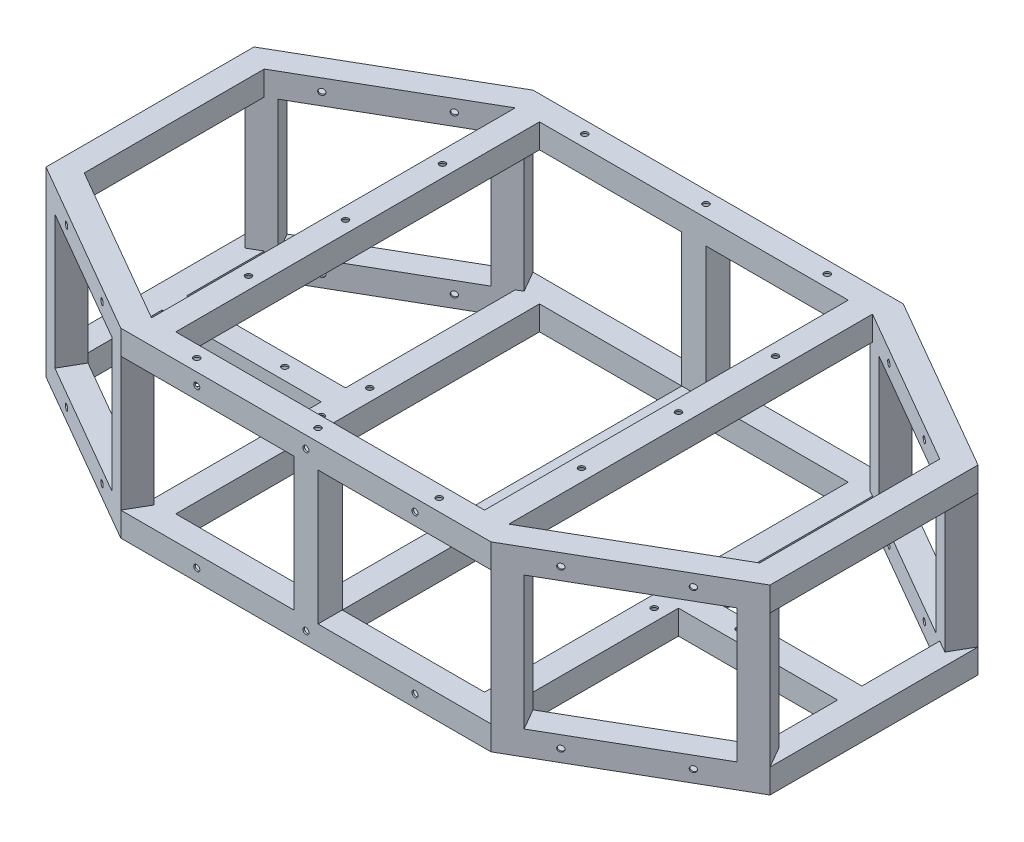
SolidWorks part; units mm, degrees
material "6061-T6 (SS)"
ref_plane "Front Plane" through (0, 0, 0) normal (0, 0, 1) x (1, 0, 0)
ref_plane "Top Plane" through (0, 0, 0) normal (0, 1, 0) x (1, 0, 0)
ref_plane "Right Plane" through (0, 0, 0) normal (1, 0, 0) x (0, 0, -1)
sketch "Sketch1" plane through (0, 0, 0) normal (1, 0, 0) x (0, 0, -1)
  line L1 (190.5, -12.7) -> (215.9, -12.7)
  line L2 (190.5, -12.7) -> (190.5, 12.7)
  line L3 (190.5, 12.7) -> (215.9, 12.7)
  line L4 (215.9, -12.7) -> (215.9, 12.7)
  line L5 (190.5, -12.7) -> (215.9, 12.7) construction
  line L6 (190.5, 12.7) -> (215.9, -12.7) construction
  line L7 (192.151, -11.049) -> (214.249, -11.049)
  line L8 (192.151, -11.049) -> (192.151, 11.049)
  line L9 (192.151, 11.049) -> (214.249, 11.049)
  line L10 (214.249, -11.049) -> (214.249, 11.049)
  line L11 (192.151, -11.049) -> (214.249, 11.049) construction
  line L12 (192.151, 11.049) -> (214.249, -11.049) construction
  point P0 (203.2, 0)
  point P5 (203.2, 0)
  dimension "D1" = 203.2
  dimension "D2" = 25.4
  dimension "D3" = 25.4
  dimension "D4" = 1.651
sketch "Sketch2" plane through (0, 0, 0) normal (0, 1, 0) x (1, 0, 0)
  line L0 (0, 0) -> (-366.4764, 0) construction
  line L1 (0, 0) -> (0, 203.2) construction
  line L2 (190.5, 203.2) -> (-190.5, 203.2)
  line L3 (-190.5, 203.2) -> (-366.4764, 101.6)
  line L4 (-366.4764, 101.6) -> (-366.4764, -101.6)
  line L5 (-366.4764, -101.6) -> (-190.5, -203.2)
  line L6 (-190.5, -203.2) -> (190.5, -203.2)
  line L7 (190.5, 203.2) -> (366.4764, 101.6)
  line L8 (366.4764, 101.6) -> (366.4764, -101.6)
  line L9 (366.4764, -101.6) -> (190.5, -203.2)
  dimension "D1" = 203.2
  dimension "D2" = 381
  dimension "D3" = 30
  dimension "D4" = 203.2
  dimension "D5" = 203.2
sweep "Sweep2" add profiles "Sketch1" path "Sketch2"
sketch "Sketch4" plane through (0, 12.7, 0) normal (0, 1, 0) x (1, 0, 0)
  line L0 (-193.903, -215.9) -> (-215.9, -203.2)
  line L1 (-193.903, -215.9) -> (-181.203, -193.903)
  line L2 (-215.9, -203.2) -> (-203.2, -181.203)
  line L3 (-181.203, -193.903) -> (-203.2, -181.203)
  line L4 (-379.1764, -108.9323) -> (-193.903, -215.9) construction
  line L5 (-213.6447, -202.5957) -> (-202.5957, -183.4583)
  line L6 (-183.4583, -194.5073) -> (-202.5957, -183.4583)
  line L7 (-194.5073, -213.6447) -> (-183.4583, -194.5073)
  line L8 (-194.5073, -213.6447) -> (-213.6447, -202.5957)
  dimension "D1" = 25.4
  dimension "D2" = 25.4
  dimension "D3" = 1.651
extrude "Vertical Member" add sketch "Sketch4" along normal blind 139.7
sketch "Sketch5" plane through (0, 12.7, 0) normal (0, 1, 0) x (1, 0, 0)
  line L0 (-379.1764, -108.9323) -> (-357.1793, -121.6323)
  line L1 (-379.1764, -108.9323) -> (-366.4764, -86.9353)
  line L2 (-357.1793, -121.6323) -> (-344.4793, -99.6353)
  line L3 (-366.4764, -86.9353) -> (-344.4793, -99.6353)
  line L4 (-379.1764, -108.9323) -> (-215.9, -203.2) construction
  line L6 (-376.9211, -108.328) -> (-357.7836, -119.377)
  line L7 (-357.7836, -119.377) -> (-346.7346, -100.2396)
  line L8 (-365.8721, -89.1906) -> (-346.7346, -100.2396)
  line L9 (-376.9211, -108.328) -> (-365.8721, -89.1906)
  dimension "D1" = 25.4
  dimension "D2" = 25.4
  dimension "D3" = 1.651
extrude "Vertical Member 2" add sketch "Sketch5" along normal blind 139.7
mirror "Mirror1" about plane through (0, 0, 0) normal (0, 0, 1) of "Vertical Member 2", "Vertical Member"
mirror "Mirror2" about plane through (0, 0, 0) normal (1, 0, 0) of "Mirror1", "Vertical Member", "Vertical Member 2"
sketch "Sketch6" plane through (0, 12.7, 0) normal (0, 1, 0) x (1, 0, 0)
  line L0 (0, -203.2) -> (0, 0) construction
  line L1 (-190.5, -203.2) -> (190.5, -203.2) construction
  line L2 (-187.097, -190.5) -> (187.097, -190.5) construction
  line L3 (-12.7, -215.9) -> (12.7, -215.9)
  line L4 (-12.7, -215.9) -> (-12.7, -190.5)
  line L5 (-12.7, -190.5) -> (12.7, -190.5)
  line L6 (12.7, -215.9) -> (12.7, -190.5)
  line L7 (-12.7, -215.9) -> (12.7, -190.5) construction
  line L8 (-12.7, -190.5) -> (12.7, -215.9) construction
  line L9 (-11.049, -192.151) -> (11.049, -192.151)
  line L10 (11.049, -214.249) -> (11.049, -192.151)
  line L11 (-11.049, -214.249) -> (11.049, -214.249)
  line L12 (-11.049, -214.249) -> (-11.049, -192.151)
  dimension "D1" = 25.4
  dimension "D2" = 1.651
extrude "Boss-Extrude3" add sketch "Sketch6" along normal blind 139.7
mirror "Mirror3" about plane through (0, 0, 0) normal (0, 0, 1) of "Boss-Extrude3"
ref_plane "Plane1" through (0, 82.55, 0) normal (0, 1, 0) x (1, 0, 0)
mirror "Mirror4" about plane through (0, 82.55, 0) normal (0, 1, 0) of "Sweep2"
sketch "Sketch7" plane through (0, 0, 190.5) normal (0, 0, -1) x (-1, 0, 0)
  line L0 (-11.049, -11.049) -> (-11.049, 11.049)
  line L1 (-12.7, -12.7) -> (12.7, -12.7)
  line L2 (-12.7, -12.7) -> (-12.7, 12.7)
  line L3 (-12.7, 12.7) -> (12.7, 12.7)
  line L4 (12.7, -12.7) -> (12.7, 12.7)
  line L5 (-12.7, -12.7) -> (12.7, 12.7) construction
  line L6 (-12.7, 12.7) -> (12.7, -12.7) construction
  line L7 (-11.049, 11.049) -> (11.049, 11.049)
  line L8 (11.049, -11.049) -> (11.049, 11.049)
  line L9 (-11.049, -11.049) -> (11.049, -11.049)
  point P0 (0, 0)
  dimension "D1" = 25.4
  dimension "D2" = 25.4
  dimension "D3" = 1.651
extrude "Boss-Extrude4" add sketch "Sketch7" along normal up to next
sketch "Sketch8" plane through (0, 0, 190.5) normal (0, 0, -1) x (-1, 0, 0)
  line L0 (-187.097, -12.7) -> (-187.097, 12.7)
  line L1 (-187.097, -12.7) -> (-161.697, -12.7)
  line L2 (-187.097, 12.7) -> (-161.697, 12.7)
  line L3 (-161.697, -12.7) -> (-161.697, 12.7)
  line L4 (-163.348, -11.049) -> (-163.348, 11.049)
  line L5 (-185.446, 11.049) -> (-163.348, 11.049)
  line L6 (-185.446, -11.049) -> (-185.446, 11.049)
  line L7 (-185.446, -11.049) -> (-163.348, -11.049)
  dimension "D1" = 25.4
  dimension "D2" = 25.4
  dimension "D3" = 1.651
extrude "Boss-Extrude5" add sketch "Sketch8" along normal up to next (381 mm away)
sketch "Sketch9" plane through (353.7764, 0, 0) normal (-1, 0, 0) x (0, 0, 1)
  line L0 (94.2677, 12.7) -> (-94.2677, 12.7) construction
  line L1 (-12.7, -12.7) -> (12.7, -12.7)
  line L2 (-12.7, -12.7) -> (-12.7, 12.7)
  line L3 (-12.7, 12.7) -> (12.7, 12.7)
  line L4 (12.7, -12.7) -> (12.7, 12.7)
  line L5 (-12.7, -12.7) -> (12.7, 12.7) construction
  line L6 (-12.7, 12.7) -> (12.7, -12.7) construction
  line L7 (-11.049, 11.049) -> (11.049, 11.049)
  line L8 (11.049, -11.049) -> (11.049, 11.049)
  line L9 (-11.049, -11.049) -> (11.049, -11.049)
  line L10 (-11.049, -11.049) -> (-11.049, 11.049)
  point P0 (0, 0)
  dimension "D1" = 25.4
  dimension "D2" = 1.651
extrude "Boss-Extrude6" add sketch "Sketch9" along normal up to next (166.6793 mm away)
mirror "Mirror5" about plane through (0, 0, 0) normal (1, 0, 0) of "Boss-Extrude5", "Boss-Extrude6"
sketch "Sketch10" plane through (0, 0, -190.5) normal (0, 0, 1) x (1, 0, 0)
  line L0 (-187.097, 177.8) -> (-187.097, 152.4)
  line L1 (-187.097, 177.8) -> (-161.697, 177.8)
  line L2 (-187.097, 152.4) -> (-161.697, 152.4)
  line L3 (-161.697, 177.8) -> (-161.697, 152.4)
  line L4 (-185.446, 154.051) -> (-163.348, 154.051)
  line L5 (-163.348, 176.149) -> (-163.348, 154.051)
  line L6 (-185.446, 176.149) -> (-163.348, 176.149)
  line L7 (-185.446, 176.149) -> (-185.446, 154.051)
  dimension "D1" = 25.4
  dimension "D2" = 25.4
  dimension "D3" = 1.651
extrude "Boss-Extrude7" add sketch "Sketch10" along normal up to next (381 mm away)
mirror "Mirror6" about plane through (0, 0, 0) normal (1, 0, 0) of "Boss-Extrude7"
sketch "Sketch12" plane through (-141.9632, 0, 245.8874) normal (-0.5, 0, 0.866) x (0.866, 0, 0.5)
  line L0 (-215.119, 165.1) -> (-113.519, 165.1) construction
  line L1 (-248.5102, 152.4) -> (-85.3749, 152.4) construction
  dimension "D1" = 12.7
  dimension "D2" = 101.6
sketch "Sketch14" plane through (-141.9632, 0, 245.8874) normal (-0.5, 0, 0.866) x (0.866, 0, 0.5)
  point P0 (-215.119, 165.1)
  point P1 (-113.519, 165.1)
hole_wizard "1/4 (0.25) Diameter Hole1" positions "Sketch18" profile "Sketch19" hole size "1/4" standard "ANSI Inch"
sketch "Sketch18" plane through (-141.9632, 0, 245.8874) normal (-0.5, 0, 0.866) x (0.866, 0, 0.5)
  point P0 (-215.119, 165.1)
  point P3 (-113.519, 165.1)
sketch "Sketch19" plane through (-328.2617, 165.1, 138.3279) normal (0, 1, 0) x (0.866, 0, 0.5)
  line L0 (0, 0) -> (0, 52.7077)
  line L1 (0, 52.7077) -> (3.175, 50.8)
  line L2 (3.175, 50.8) -> (3.175, 0)
  line L5 (3.175, 0) -> (0, 0)
  line L10 (0, 52.7077) -> (-3.175, 50.8) construction
  line L11 (0, -6.35) -> (0, 107.95) construction
  dimension "Hole Dia." = 6.35
  dimension "Hole Depth" = 50.8
  dimension "Drill Angle" = 118
mirror "Mirror7" about plane through (0, 82.55, 0) normal (0, 1, 0) of "1/4 (0.25) Diameter Hole1"
mirror "Mirror8" about plane through (0, 0, 0) normal (0, 0, 1) of "Mirror7", "1/4 (0.25) Diameter Hole1"
mirror "Mirror9" about plane through (0, 0, 0) normal (1, 0, 0) of "Mirror8", "Mirror7", "1/4 (0.25) Diameter Hole1"
sketch "Sketch20" plane through (0, 12.7, 0) normal (0, 1, 0) x (1, 0, 0)
  line L0 (-161.697, -190.5) -> (-12.7, -190.5) construction
  line L1 (-187.097, -190.5) -> (-187.097, 190.5) construction
  line L2 (-187.097, 190.5) -> (-187.097, 12.7) construction
  line L3 (-187.097, 12.7) -> (-353.7764, 12.7) construction
  line L4 (-12.7, 190.5) -> (-161.697, 190.5) construction
  circle A0 centre (-174.397, -25.4) radius 3.175
  circle A2 centre (-237.897, 0) radius 3.175
  circle A3 centre (-174.397, 25.4) radius 3.175
  dimension "D6" = 6.35
  dimension "D7" = 12.7
  dimension "D8" = 6.35
  dimension "D4" = 6.35
  dimension "D1" = 165.1
  dimension "D2" = 165.1
  dimension "D3" = 12.7
  dimension "D5" = 50.8
  dimension "D9" = 12.7
extrude "Cut-Extrude1" cut sketch "Sketch20" against normal up to next (1.651 mm away)
mirror "Mirror10" about plane through (0, 0, 0) normal (1, 0, 0) of "Cut-Extrude1"
sketch "Sketch21" plane through (0, 177.8, 0) normal (0, 1, 0) x (1, 0, 0)
  line L0 (-161.697, -190.5) -> (-161.697, 190.5) construction
  line L1 (-161.697, -190.5) -> (161.697, -190.5) construction
  line L3 (0, -104.775) -> (0, 104.775) construction
  line L4 (-104.775, 0) -> (104.775, 0) construction
  circle A0 centre (-174.397, 101.6) radius 3.175
  circle A4 centre (-174.397, 0) radius 3.175
  circle A5 centre (-174.397, -101.6) radius 3.175
  circle A6 centre (-127, -203.2) radius 3.175
  circle A7 centre (0, -203.2) radius 3.175
  circle A8 centre (127, -203.2) radius 3.175
  circle A9 centre (174.397, 101.6) radius 3.175
  circle A10 centre (174.397, 0) radius 3.175
  circle A11 centre (174.397, -101.6) radius 3.175
  circle A12 centre (127, 203.2) radius 3.175
  circle A13 centre (0, 203.2) radius 3.175
  circle A14 centre (-127, 203.2) radius 3.175
  dimension "D1" = 6.35
  dimension "D2" = 6.35
  dimension "D3" = 6.35
  dimension "D4" = 6.35
  dimension "D5" = 6.35
  dimension "D6" = 6.35
  dimension "D10" = 12.7
  dimension "D11" = 12.7
  dimension "D12" = 12.7
  dimension "D13" = 12.7
  dimension "D14" = 12.7
  dimension "D15" = 12.7
  dimension "D19" = 101.6
  dimension "D20" = 101.6
  dimension "D21" = 101.6
  dimension "D22" = 127
  dimension "D23" = 127
extrude "Cut-Extrude2" cut sketch "Sketch21" against normal blind 50.8
sketch "Sketch22" plane through (0, 0, 215.9) normal (0, 0, 1) x (1, 0, 0)
  line L0 (-193.903, 177.8) -> (193.903, 177.8) construction
  line L3 (-193.903, -12.7) -> (193.903, -12.7) construction
  circle A0 centre (-114.3, 165.1) radius 3.175
  circle A1 centre (0, 165.1) radius 3.175
  circle A2 centre (114.3, 165.1) radius 3.175
  circle A3 centre (-114.3, 0) radius 3.175
  circle A4 centre (0, 0) radius 3.175
  circle A5 centre (114.3, 0) radius 3.175
  point P17 (0, 0)
  point P18 (0, 0)
  dimension "D4" = 6.35
  dimension "D5" = 6.35
  dimension "D6" = 6.35
  dimension "D7" = 6.35
  dimension "D10" = 6.35
  dimension "D12" = 6.35
  dimension "D1" = 12.7
  dimension "D2" = 12.7
  dimension "D3" = 12.7
  dimension "D8" = 12.7
  dimension "D9" = 12.7
  dimension "D11" = 12.7
  dimension "D13" = 114.3
  dimension "D14" = 114.3
  dimension "D15" = 114.3
  dimension "D16" = 114.3
extrude "Cut-Extrude3" cut sketch "Sketch22" against normal up to next
